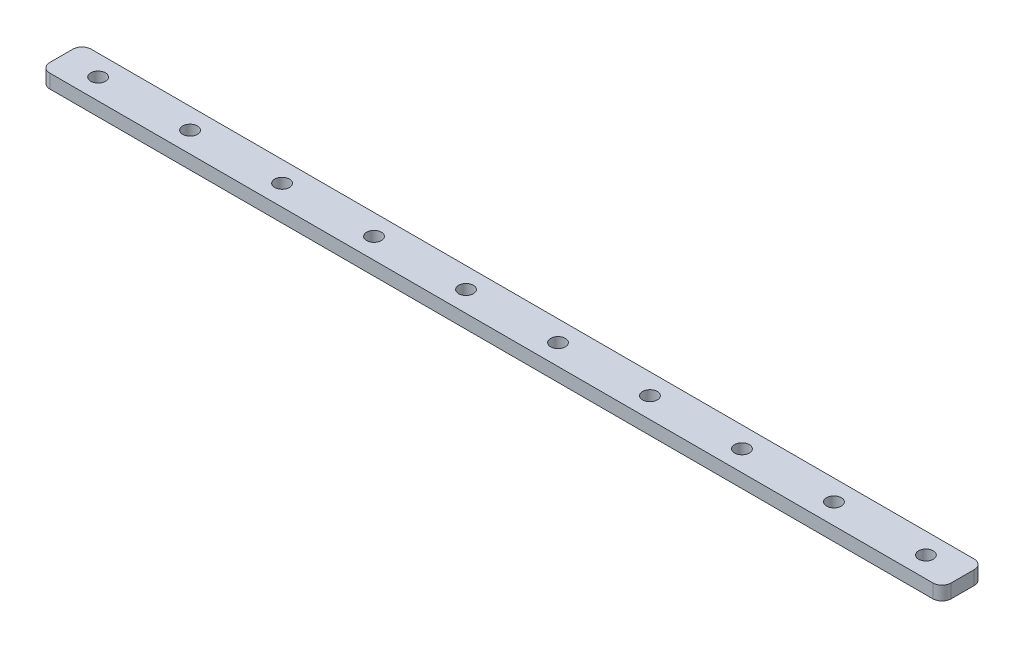
SolidWorks part; units mm, degrees
material "A-玻璃纤维"
ref_plane "前视基准面" through (0, 0, 0) normal (0, 0, 1) x (1, 0, 0)
ref_plane "上视基准面" through (0, 0, 0) normal (0, 1, 0) x (1, 0, 0)
ref_plane "右视基准面" through (0, 0, 0) normal (1, 0, 0) x (0, 0, -1)
sketch "草图1" plane through (0, 0, 0) normal (0, 1, 0) x (1, 0, 0)
  line L0 (0, 4.5) -> (8, 4.5) construction
  line L1 (0, 0) -> (196, 0)
  line L2 (0, 0) -> (0, 9)
  line L3 (0, 9) -> (196, 9)
  line L4 (196, 0) -> (196, 9)
  circle A0 centre (8, 4.5) radius 1.6
  circle A1 centre (28, 4.5) radius 1.6
  circle A2 centre (48, 4.5) radius 1.6
  circle A3 centre (68, 4.5) radius 1.6
  circle A4 centre (88, 4.5) radius 1.6
  circle A5 centre (108, 4.5) radius 1.6
  circle A6 centre (128, 4.5) radius 1.6
  circle A7 centre (148, 4.5) radius 1.6
  circle A8 centre (168, 4.5) radius 1.6
  circle A9 centre (188, 4.5) radius 1.6
  dimension "D2" = 3.2
  dimension "D5" = 8
  dimension "D6" = 40
  dimension "D1" = 9
  dimension "D3" = 8
  dimension "D4" = 10
extrude "凸台-拉伸1" add sketch "草图1" along normal blind 3
fillet "圆角1" radius 2 4 edges at (0, 1.5, -9) (0, 1.5, 0) (196, 1.5, -9) (196, 1.5, 0)
